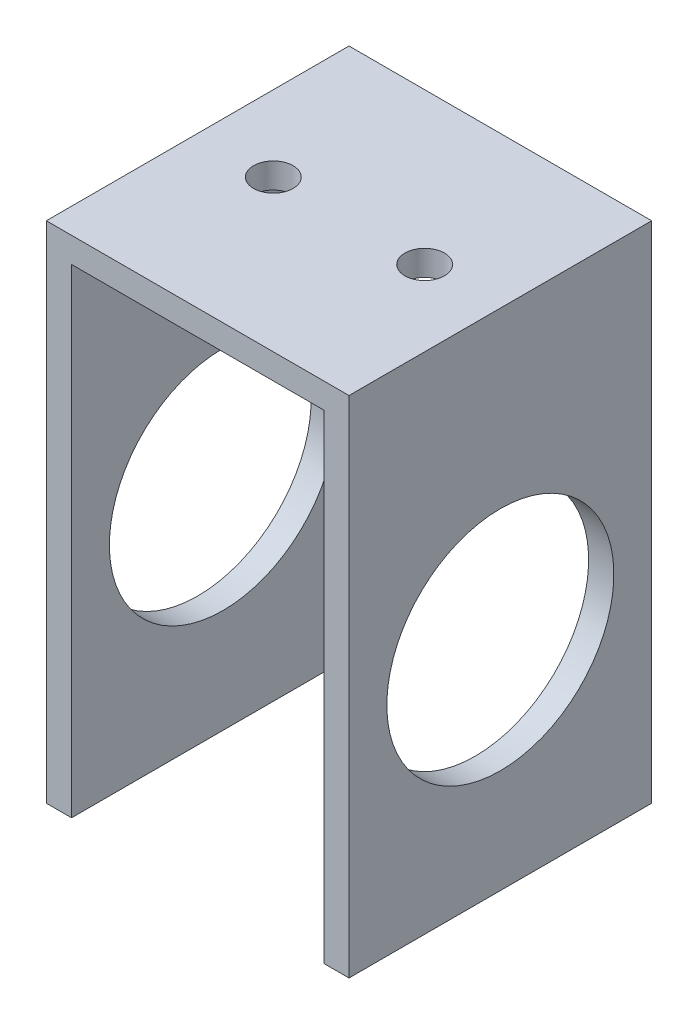
SolidWorks part; units mm, degrees
material "6061-T6 (SS)"
ref_plane "Front Plane" through (0, 0, 0) normal (0, 0, 1) x (1, 0, 0)
ref_plane "Top Plane" through (0, 0, 0) normal (0, 1, 0) x (1, 0, 0)
ref_plane "Right Plane" through (0, 0, 0) normal (1, 0, 0) x (0, 0, -1)
sketch "Sketch1" plane through (0, 0, 0) normal (0, 0, 1) x (1, 0, 0)
  line L0 (-19.05, 0) -> (19.05, 0)
  line L1 (19.05, 0) -> (19.05, -63.5)
  line L2 (19.05, -63.5) -> (15.875, -63.5)
  line L3 (15.875, -63.5) -> (15.875, -3.175)
  line L4 (15.875, -3.175) -> (-15.875, -3.175)
  line L5 (-15.875, -3.175) -> (-15.875, -63.5)
  line L6 (-15.875, -63.5) -> (-19.05, -63.5)
  line L7 (-19.05, -63.5) -> (-19.05, 0)
  line L8 (0, 0) -> (0, -3.175) construction
  point P3 (0, 0)
  dimension "D1" = 63.5
  dimension "D2" = 3.175
  dimension "D3" = 38.1
extrude "Boss-Extrude1" add sketch "Sketch1" along normal blind 38.1
sketch "Sketch2" plane through (19.05, 0, 0) normal (1, 0, 0) x (0, 0, -1)
  line L0 (-19.05, -63.5) -> (-19.05, -36.15) construction
  line L1 (-38.1, -63.5) -> (0, -63.5) construction
  circle A0 centre (-19.05, -36.15) radius 14.2875
  dimension "D1" = 28.575
  dimension "D2" = 27.35
extrude "Cut-Extrude1" cut sketch "Sketch2" against normal through all
sketch "Sketch3" plane through (0, 0, 0) normal (0, 1, 0) x (1, 0, 0)
  line L0 (-19.05, -38.1) -> (-19.05, 0) construction
  line L3 (-19.05, -31.75) -> (19.05, -31.75) construction
  line L4 (-19.05, -31.75) -> (-19.05, -6.35) construction
  line L5 (-19.05, -6.35) -> (19.05, -6.35) construction
  line L6 (19.05, -31.75) -> (19.05, -6.35) construction
  line L7 (19.05, -38.1) -> (19.05, 0) construction
  line L8 (-19.05, -19.05) -> (19.05, -19.05) construction
  point P8 (-19.05, -19.05)
  point P10 (-19.05, -19.05)
  point P13 (-9.525, -19.05)
  point P14 (9.525, -19.05)
  dimension "D1" = 25.4
  dimension "D2" = 19.05
  dimension "D3" = 9.525
hole_wizard "#9 (0.196) Diameter Hole1" positions "Sketch4" profile "Sketch5" hole size "#9" standard "ANSI Inch" end condition up to next
sketch "Sketch4" plane through (0, 0, 0) normal (0, 1, 0) x (1, 0, 0)
  point P0 (-9.525, -19.05)
  point P3 (9.525, -19.05)
sketch "Sketch5" plane through (-9.525, 0, 19.05) normal (1, 0, 0) x (0, 0, 1)
  line L0 (0, 0) -> (0, 3.175)
  line L1 (0, 3.175) -> (2.4892, 3.175)
  line L2 (2.4892, 3.175) -> (2.4892, 0)
  line L5 (2.4892, 0) -> (0, 0)
  line L11 (0, -6.35) -> (0, 107.95) construction
  dimension "Thru Hole Dia." = 4.9784
  dimension "Thru Hole Depth" = 3.175
equation "\"Thick\"= \"in\""
